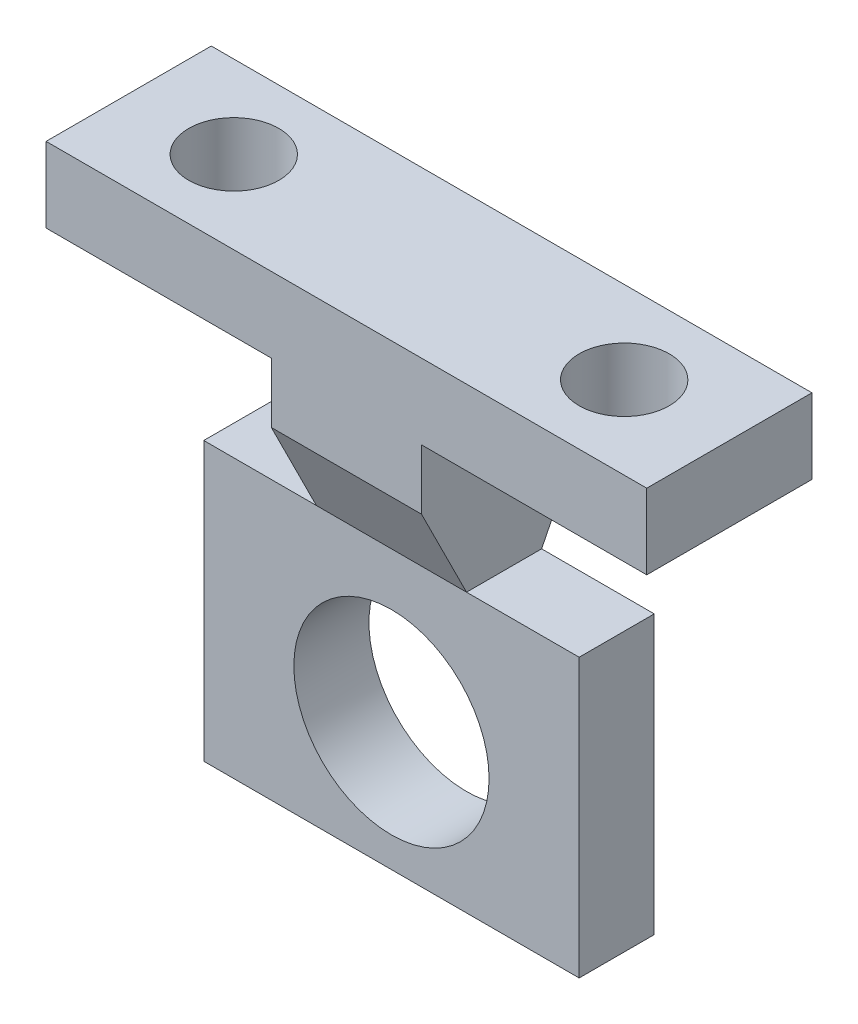
SolidWorks part; units mm, degrees
ref_plane "Front Plane" through (0, 0, 0) normal (0, 0, 1) x (1, 0, 0)
ref_plane "Top Plane" through (0, 0, 0) normal (0, 1, 0) x (1, 0, 0)
ref_plane "Right Plane" through (0, 0, 0) normal (1, 0, 0) x (0, 0, -1)
sketch "Sketch1" plane through (0, 0, 0) normal (0, 0, 1) x (1, 0, 0)
  line L0 (0, 0) -> (40, 0)
  line L1 (40, 0) -> (40, 50)
  line L2 (0, 0) -> (0, 50)
  line L3 (0, 50) -> (40, 50)
extrude "Boss-Extrude1" add sketch "Sketch1" along normal blind 15 and the other way blind 0.0001
sketch "Sketch2" plane through (0, 0, 15) normal (0, 0, 1) x (1, 0, 0)
  circle A0 centre (20, 10) radius 6.5
extrude "Cut-Extrude1" cut sketch "Sketch2" against normal blind 30 contours A0
sketch "Sketch3" plane through (0, 0, -0.0001) normal (0, 0, -1) x (-1, 0, 0)
  line L1 (-40, 0) -> (-40, 50) construction
  line L2 (-40, 45) -> (-25, 45)
  line L3 (-25, 45) -> (-25, 35)
  line L4 (-25, 35) -> (-40, 35)
  line L5 (-40, 35) -> (-40, 45)
  line L7 (0, 50) -> (0, 0) construction
  line L8 (0, 45) -> (-15, 45)
  line L9 (-15, 45) -> (-15, 35)
  line L10 (-15, 35) -> (0, 35)
  line L11 (0, 35) -> (0, 45)
extrude "Cut-Extrude4" cut sketch "Sketch3" against normal blind 30
sketch "Sketch5" plane through (0, 50, 0) normal (0, 1, 0) x (1, 0, 0)
  circle A0 centre (7, -7.5) radius 3
  circle A1 centre (33, -7.5) radius 3
extrude "Cut-Extrude5" cut sketch "Sketch5" against normal blind 10
sketch "Sketch6" plane through (0, 0, 15) normal (0, 0, 1) x (1, 0, 0)
  line L0 (0, 35) -> (40, 35)
  line L1 (40, 35) -> (40, 0)
  line L2 (40, 0) -> (0, 0)
  line L3 (0, 0) -> (0, 35)
extrude "Cut-Extrude7" cut sketch "Sketch6" against normal blind 3.5
sketch "Sketch7" plane through (0, 0, -0.0001) normal (0, 0, -1) x (-1, 0, 0)
  line L0 (-40, 35) -> (0, 35)
  line L1 (0, 35) -> (0, 0)
  line L2 (0, 0) -> (-40, 0)
  line L3 (-40, 0) -> (-40, 35)
extrude "Cut-Extrude8" cut sketch "Sketch7" against normal blind 3.5
sketch "Sketch8" plane through (15, 0, 0) normal (-1, 0, 0) x (0, 0, 1)
  line L0 (-0.0001, 35) -> (3.4999, 35)
  line L1 (3.4999, 35) -> (-0.0001, 45)
  line L2 (-0.0001, 45) -> (-0.0001, 35)
  line L3 (11.5, 35) -> (15, 35)
  line L4 (15, 35) -> (15, 45)
  line L5 (15, 45) -> (11.5, 35)
extrude "Cut-Extrude9" cut sketch "Sketch8" against normal blind 15
sketch "Sketch10" plane through (0, 0, 11.5) normal (0, 0, 1) x (1, 0, 0)
  line L0 (0, 35) -> (40, 35)
  line L1 (40, 35) -> (40, 0)
  line L2 (40, 0) -> (0, 0)
  line L3 (0, 0) -> (0, 35)
  circle A3 centre (20, 10) radius 6.5
  circle A5 centre (20, 25.0017) radius 6.5
extrude "Cut-Extrude11" cut sketch "Sketch10" against normal blind 10 contours A5
sketch "Sketch11" plane through (0, 0, 11.5) normal (0, 0, 1) x (1, 0, 0)
  line L0 (0, 35) -> (0, 17.5)
  line L1 (0, 35) -> (0, 0) construction
  line L2 (0, 16.5) -> (40, 16.5)
  line L4 (40, 16.5) -> (40, 35)
  line L5 (40, 35) -> (0, 35)
  line L6 (0, 16.5) -> (0, 0)
  line L7 (0, 0) -> (40, 0)
  line L8 (40, 0) -> (40, 16.5)
extrude "Cut-Extrude16" cut sketch "Sketch11" against normal blind 10 contours L8 L7 L6 L2
sketch "Sketch12" plane through (0, 0, 11.5) normal (0, 0, 1) x (1, 0, 0)
  line L0 (0, 35) -> (40, 35)
  line L1 (40, 35) -> (40, 16.5)
  line L2 (40, 16.5) -> (0, 16.5)
  line L3 (0, 16.5) -> (0, 35)
extrude "Cut-Extrude17" cut sketch "Sketch12" against normal blind 1.5
sketch "Sketch13" plane through (0, 0, 3.4999) normal (0, 0, -1) x (-1, 0, 0)
  line L0 (-40, 35) -> (0, 35)
  line L1 (0, 35) -> (0, 16.5)
  line L2 (0, 16.5) -> (-40, 16.5)
  line L3 (-40, 16.5) -> (-40, 35)
extrude "Cut-Extrude18" cut sketch "Sketch13" against normal blind 1.5
sketch "Sketch14" plane through (15, 0, 0) normal (-1, 0, 0) x (0, 0, 1)
  line L0 (4.9999, 35) -> (-0.0001, 45)
  line L1 (-0.0001, 45) -> (3.4999, 35)
  line L2 (3.4999, 35) -> (4.9999, 35)
  line L3 (10, 35) -> (11.5, 35)
  line L4 (11.5, 35) -> (10, 35) construction
  line L5 (15, 45) -> (11.5, 35) construction
  line L6 (11.5, 35) -> (15, 45)
  line L7 (15, 45) -> (10, 35)
extrude "Cut-Extrude19" cut sketch "Sketch14" against normal blind 150
sketch "Sketch15" plane through (0, 50, 0) normal (0, 1, 0) x (1, 0, 0)
  line L0 (0, 0) -> (0, -2)
  line L1 (0, 0.0001) -> (0, -15) construction
  line L2 (0, -2) -> (40, -2)
  line L3 (40, 0.0001) -> (40, -15) construction
  line L4 (40, -2) -> (40, 0.0001)
  line L5 (40, 0.0001) -> (0, 0)
  line L6 (0, -15) -> (0, -13)
  line L7 (0, -13) -> (40, -13)
  line L8 (0, -15) -> (40, -15)
  line L9 (40, -15) -> (0, -15) construction
  line L10 (40, -15) -> (40, -13)
extrude "Cut-Extrude21" cut sketch "Sketch15" against normal blind 10
sketch "Sketch16" plane through (0, 0, -0.0001) normal (0, 0, -1) x (-1, 0, 0)
  line L0 (0, 50) -> (0, 45)
  line L1 (0, 45) -> (-40, 45)
  line L2 (-40, 45) -> (-40, 50)
  line L3 (-40, 50) -> (0, 50)
extrude "Cut-Extrude22" cut sketch "Sketch16" against normal blind 1
sketch "Sketch17" plane through (0, 0, 4.9999) normal (0, 0, -1) x (-1, 0, 0)
  line L7 (-40, 35) -> (-32.5, 35)
  line L26 (-25, 35) -> (-40, 35) construction
  line L27 (-32.5, 35) -> (-32.5, 16.5)
  line L28 (-32.5, 16.5) -> (-40, 16.5)
  line L29 (-40, 16.5) -> (-40, 35)
  line L34 (0, 16.5) -> (0, 35)
  line L35 (0, 35) -> (-7.5, 35)
  line L36 (-7.5, 35) -> (-7.5, 16.5)
  line L37 (-7.5, 16.5) -> (0, 16.5)
extrude "Cut-Extrude23" cut sketch "Sketch17" against normal blind 10
